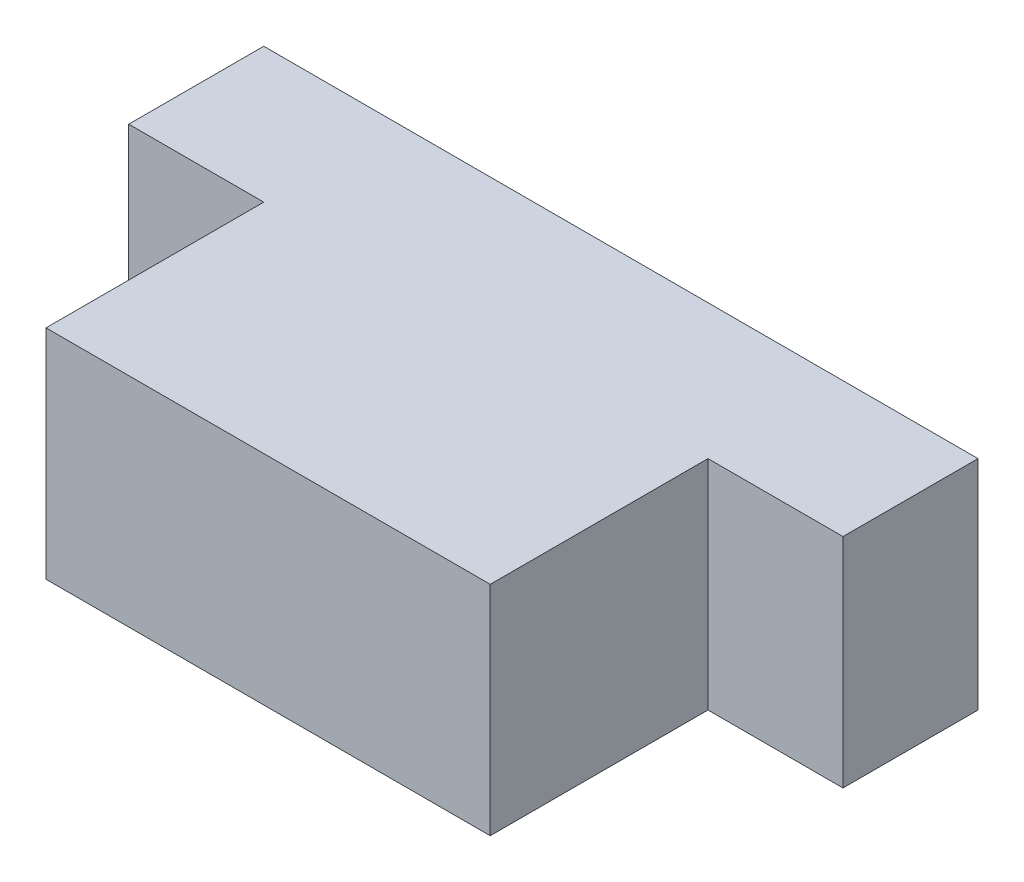
SolidWorks part; units mm, degrees
ref_plane "前视基准面" through (0, 0, 0) normal (0, 0, 1) x (1, 0, 0)
ref_plane "上视基准面" through (0, 0, 0) normal (0, 1, 0) x (1, 0, 0)
ref_plane "右视基准面" through (0, 0, 0) normal (1, 0, 0) x (0, 0, -1)
sketch "草图1" plane through (0, 0, 0) normal (0, 1, 0) x (1, 0, 0)
  line L0 (0, 5) -> (0, 0)
  line L1 (0, 0) -> (10.2, 0)
  line L2 (10.2, 0) -> (10.2, 5)
  line L3 (10.2, 5) -> (13.3, 5)
  line L4 (13.3, 5) -> (13.3, 8.1)
  line L5 (13.3, 8.1) -> (-3.1, 8.1)
  line L6 (-3.1, 8.1) -> (-3.1, 5)
  line L7 (-3.1, 5) -> (0, 5)
  dimension "D1" = 10.2
  dimension "D2" = 5
  dimension "D3" = 3.1
  dimension "D4" = 3.1
  dimension "D5" = 3.1
  dimension "D6" = 5
extrude "凸台-拉伸1" add sketch "草图1" along normal blind 5
